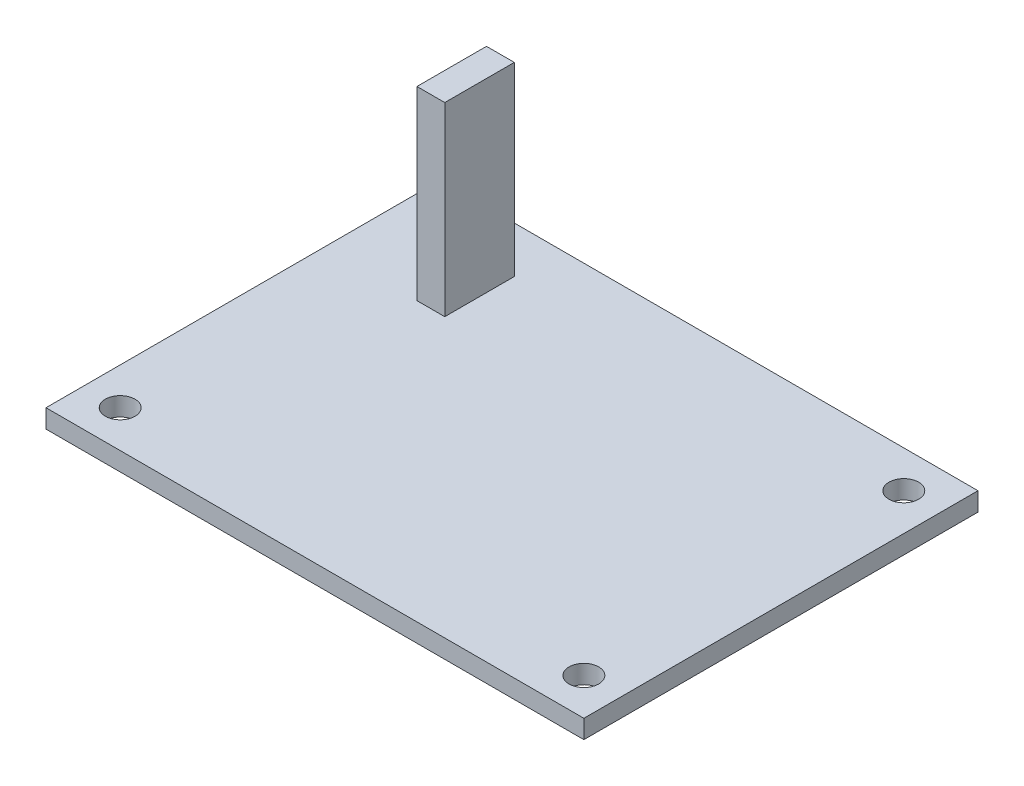
SolidWorks part; units mm, degrees
ref_plane "前视基准面" through (0, 0, 0) normal (0, 0, 1) x (1, 0, 0)
ref_plane "上视基准面" through (0, 0, 0) normal (0, 1, 0) x (1, 0, 0)
ref_plane "右视基准面" through (0, 0, 0) normal (1, 0, 0) x (0, 0, -1)
sketch "草图1" plane through (0, 0, 0) normal (0, 1, 0) x (1, 0, 0)
  line L1 (0, 0) -> (58, 0)
  line L2 (0, 0) -> (0, 42.5)
  line L3 (0, 42.5) -> (58, 42.5)
  line L4 (58, 0) -> (58, 42.5)
  dimension "D1" = 58
  dimension "D2" = 42.5
extrude "凸台-拉伸1" add sketch "草图1" along normal blind 2
sketch "草图2" plane through (0, 2, 0) normal (0, 1, 0) x (1, 0, 0)
  line L0 (0, 21.25) -> (61.6674, 21.25) construction
  line L1 (0, 42.5) -> (0, 0) construction
  line L2 (29, 42.5) -> (29, 13.1632) construction
  line L3 (58, 42.5) -> (0, 42.5) construction
  line L6 (58, 0) -> (58, 42.5) construction
  circle A0 centre (54, 38.5) radius 1.6
  circle A1 centre (54, 4) radius 1.6
  circle A2 centre (4, 4) radius 1.6
  circle A3 centre (4, 38.5) radius 1.6
  point P12 (58, 40.2615)
  point P13 (58, 39.6641)
  dimension "D1" = 3.2
  dimension "D2" = 4
  dimension "D3" = 4
extrude "切除-拉伸1" cut sketch "草图2" against normal through all
sketch "草图3" plane through (0, 2, 0) normal (0, 1, 0) x (1, 0, 0)
  line L0 (0, 42.5) -> (0, 0) construction
  line L1 (10, 37.5) -> (13, 37.5)
  line L2 (10, 37.5) -> (10, 30)
  line L3 (10, 30) -> (13, 30)
  line L4 (13, 37.5) -> (13, 30)
  line L5 (58, 42.5) -> (0, 42.5) construction
  dimension "D1" = 3
  dimension "D2" = 7.5
  dimension "D3" = 10
  dimension "D4" = 5
extrude "凸台-拉伸2" add sketch "草图3" along normal blind 20
